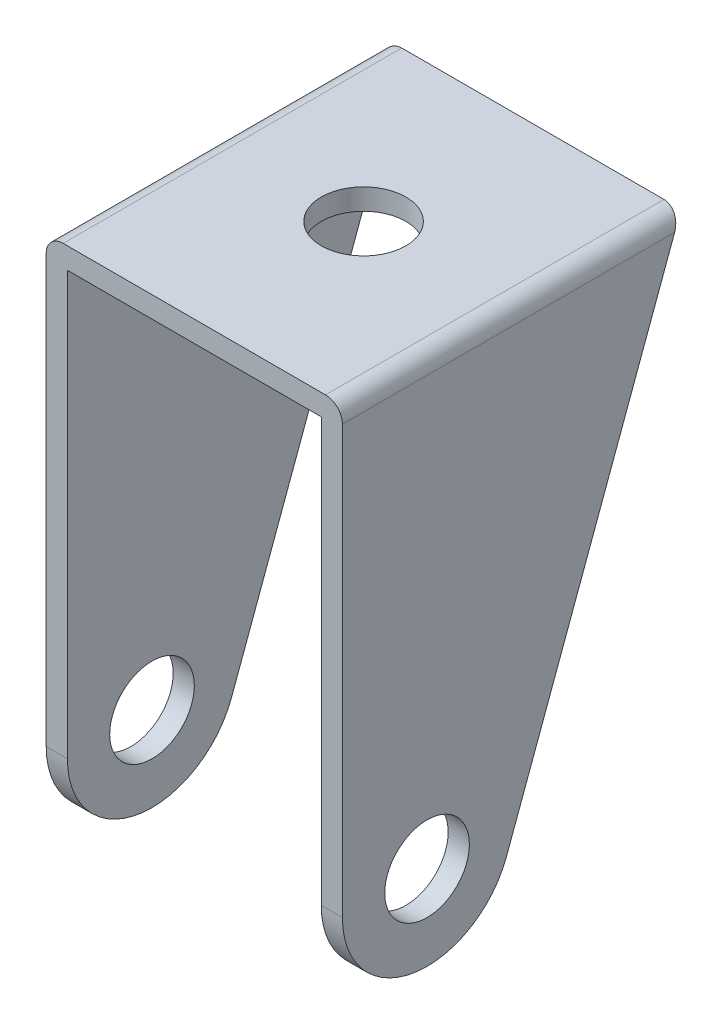
SolidWorks part; units mm, degrees
ref_plane "Alzado" through (0, 0, 0) normal (0, 0, 1) x (1, 0, 0)
ref_plane "Planta" through (0, 0, 0) normal (0, 1, 0) x (1, 0, 0)
ref_plane "Vista lateral" through (0, 0, 0) normal (1, 0, 0) x (0, 0, -1)
sketch "Croquis3" plane through (0, 0, 0) normal (0, 0, 1) x (1, 0, 0)
  line L0 (0, 0) -> (0, 76.2)
  line L1 (0, 76.2) -> (38.1, 76.2)
  line L2 (38.1, 76.2) -> (38.1, 0)
  line L3 (0, 0) -> (-3.175, 0)
  line L4 (-3.175, 0) -> (-3.175, 79.375)
  line L5 (-3.175, 79.375) -> (41.275, 79.375)
  line L6 (41.275, 79.375) -> (41.275, 0)
  line L7 (41.275, 0) -> (38.1, 0)
  dimension "D1" = 76.2
  dimension "D2" = 38.1
  dimension "D3" = 3.175
  dimension "D4" = 3.175
  dimension "D5" = 3.175
extrude "Saliente-Extruir1" add sketch "Croquis3" along normal blind 50.8
sketch "Croquis4" plane through (41.275, 0, 0) normal (1, 0, 0) x (0, 0, -1)
  line L0 (0, 79.375) -> (-26.1831, 8.3094)
  line L1 (-50.8, 0) -> (-50.8, 79.375) construction
  line L2 (-50.8, 0) -> (0, 0) construction
  line L3 (-50.8, 12.7) -> (-50.8, 0)
  line L4 (-50.8, 0) -> (0, 0)
  line L5 (0, 0) -> (0, 79.375)
  arc A0 (-26.1831, 8.3094) -> (-50.8, 12.7) centre (-38.1, 12.7) cw
  circle A1 centre (-38.1, 12.7) radius 6.35
  line M1 (0, 0) -> (0, 79.375)
  line M3 (-50.8, 79.375) -> (-50.8, 0)
  line M4 (-50.8, 0) -> (0, 0)
  dimension "D1" = 12.7
  dimension "D2" = 12.7
extrude "Cortar-Extruir4" cut sketch "Croquis4" against normal blind 50.8 contours A0 M4 M3 | A1 | L0 A0 L4 M1
fillet "Redondeo1" radius 2.54 2 edges at (41.275, 79.375, 25.4) (-3.175, 79.375, 25.4)
sketch "Croquis7" plane through (0, 79.375, 0) normal (0, 1, 0) x (1, 0, 0)
  circle A0 centre (19.05, -25.4) radius 6.35
  dimension "D1" = 12.7
extrude "Cortar-Extruir5" cut sketch "Croquis7" against normal up to vertex (3.175 mm away) up to point (38.1, 76.2, 50.8)
